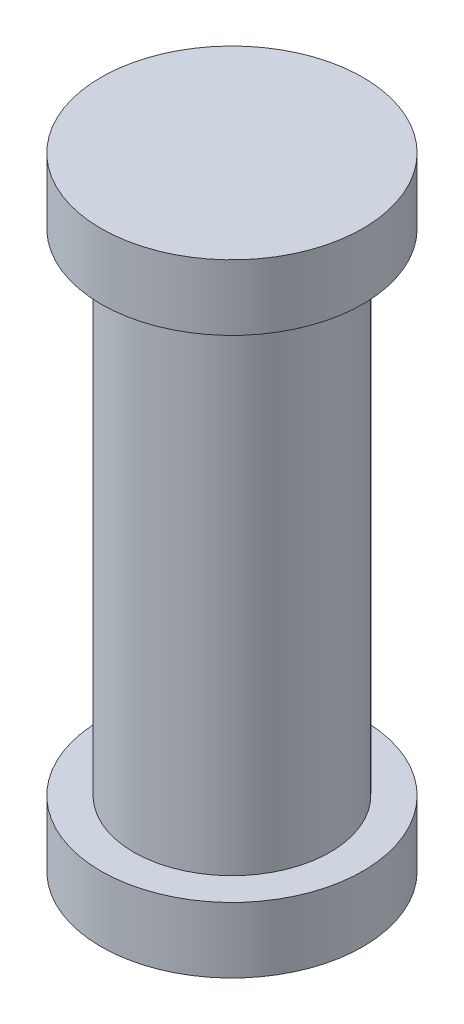
SolidWorks part; units mm, degrees
ref_plane "Front Plane" through (0, 0, 0) normal (0, 0, 1) x (1, 0, 0)
ref_plane "Top Plane" through (0, 0, 0) normal (0, 1, 0) x (1, 0, 0)
ref_plane "Right Plane" through (0, 0, 0) normal (1, 0, 0) x (0, 0, -1)
sketch "Sketch1" plane through (0, 0, 0) normal (0, 1, 0) x (1, 0, 0)
  circle A0 centre (0, 0) radius 1.6
extrude "Boss-Extrude1" add sketch "Sketch1" along normal blind 0.8
sketch "Sketch2" plane through (0, 0.8, 0) normal (0, 1, 0) x (1, 0, 0)
  circle A0 centre (0, 0) radius 1.2
extrude "Boss-Extrude2" add sketch "Sketch2" along normal blind 6
sketch "Sketch3" plane through (0, 6.8, 0) normal (0, 1, 0) x (1, 0, 0)
  circle A0 centre (0, 0) radius 1.6
extrude "Boss-Extrude3" add sketch "Sketch3" along normal blind 0.8
